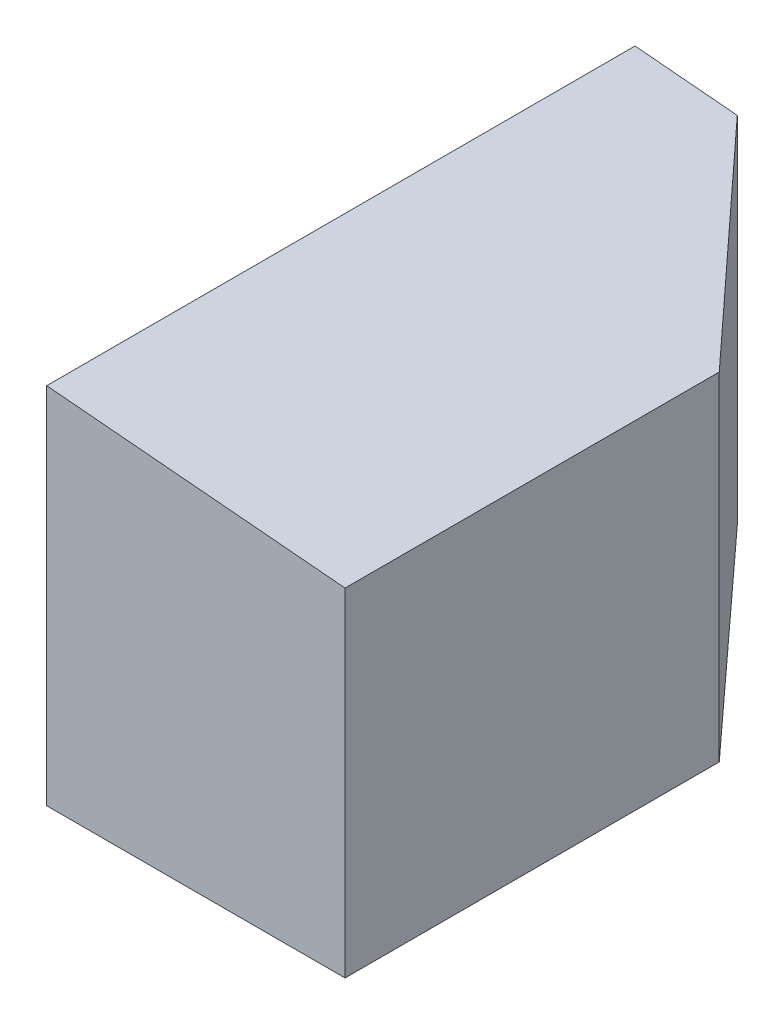
SolidWorks part; units mm, degrees
ref_plane "Ebene vorne" through (0, 0, 0) normal (0, 0, 1) x (1, 0, 0)
ref_plane "Ebene oben" through (0, 0, 0) normal (0, 1, 0) x (1, 0, 0)
ref_plane "Ebene rechts" through (0, 0, 0) normal (1, 0, 0) x (0, 0, -1)
sketch "Skizze1" plane through (0, 0, 0) normal (0, 1, 0) x (1, 0, 0)
  line L3 (-2500, 4930) -> (-2500, 0)
  line L9 (-2500, 0) -> (0, 0)
  line L10 (0, 3135.5476) -> (0, 0)
  line L11 (-2500, 4930) -> (-1643.2248, 4930)
  line L12 (-1643.2248, 4930) -> (0, 3135.5476)
  dimension "D1" = 2500
  dimension "D2" = 4930
  dimension "D3" = 2433.1559
  dimension "D4" = 856.7752
extrude "Aufsatz-Linear austragen1" add sketch "Skizze1" along normal blind 3048.54
sketch "Skizze2" plane through (0, 0, 0) normal (0, 0, 1) x (1, 0, 0)
  line L0 (-2500, 3048.54) -> (0, 2829.8183)
  line L1 (0, 3048.54) -> (0, 0) construction
  line L2 (-2500, 3048.54) -> (0, 3048.54)
  line L3 (0, 3048.54) -> (0, 2829.8183)
  dimension "D1" = 5
extrude "Schnitt-Linear austragen1" cut sketch "Skizze2" against normal through all
sketch "Skizze3" plane through (0, 0, 0) normal (0, 0, 1) x (1, 0, 0)
  line L0 (0, 2829.8183) -> (0, 0) construction
  line L1 (14, 2656) -> (14, 2770)
  line L2 (206, 2770) -> (14, 2770) construction
  line L3 (110, 2770) -> (110, 2656) construction
  line L4 (110, 2656) -> (14, 2656)
  line L5 (-2500, 0) -> (0, 0) construction
  line L6 (19, 2661) -> (19, 2770)
  line L7 (201, 2770) -> (206, 2770)
  line L8 (201, 2661) -> (201, 2770)
  line L9 (206, 2656) -> (206, 2770)
  line L10 (14, 2770) -> (19, 2770)
  line L11 (110, 2656) -> (206, 2656)
  line L12 (110, 2661) -> (19, 2661)
  line L13 (110, 2661) -> (201, 2661)
  dimension "D1" = 182
  dimension "D2" = 192
  dimension "D3" = 114
  dimension "D5" = 110
  dimension "D8" = 5
  dimension "D4" = 91
  dimension "D6" = 2770
  dimension "D7" = 96
